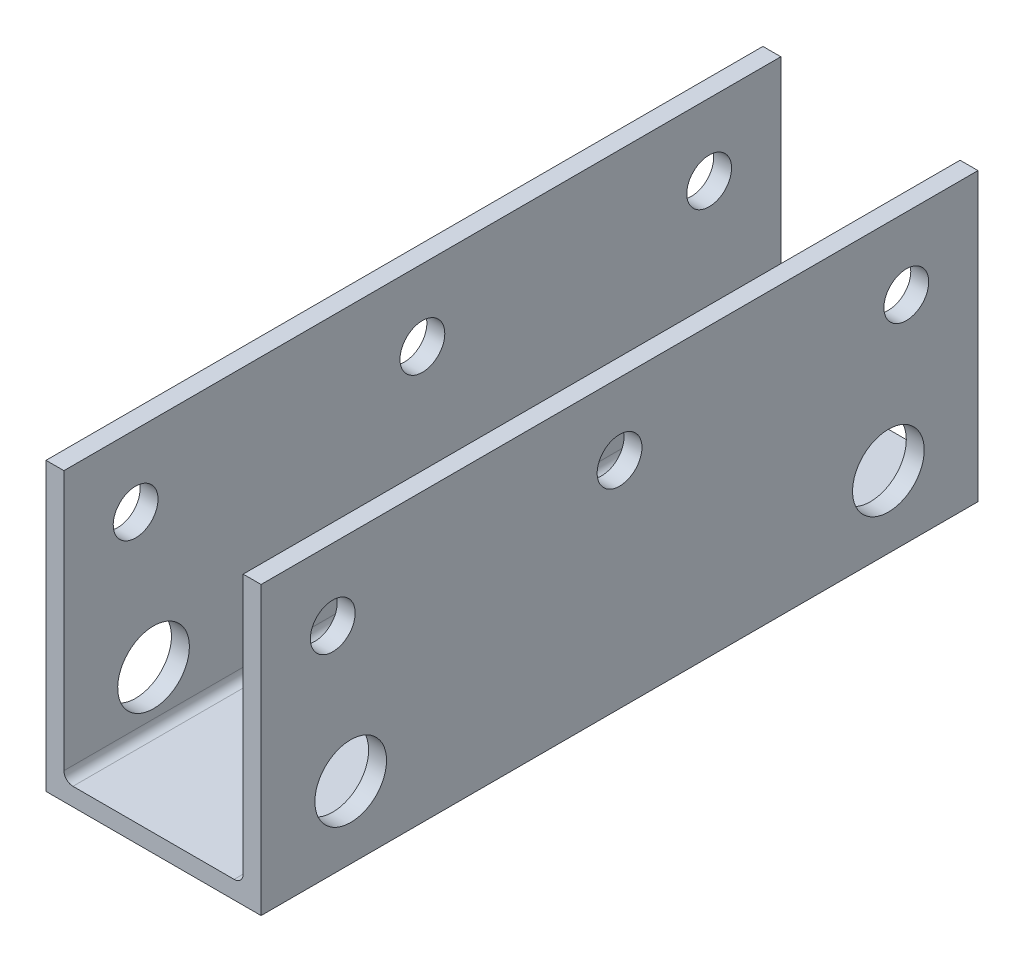
SolidWorks part; units mm, degrees
material "6061-T6 (SS)"
ref_plane "Front Plane" through (0, 0, 0) normal (0, 0, 1) x (1, 0, 0)
ref_plane "Top Plane" through (0, 0, 0) normal (0, 1, 0) x (1, 0, 0)
ref_plane "Right Plane" through (0, 0, 0) normal (1, 0, 0) x (0, 0, -1)
sketch "Sketch1" plane through (0, 0, 0) normal (0, 0, 1) x (1, 0, 0)
  line L0 (3.175, 50.8) -> (3.175, 3.175)
  line L1 (0, 0) -> (38.1, 0)
  line L2 (0, 0) -> (0, 50.8)
  line L3 (0, 50.8) -> (3.175, 50.8)
  line L4 (38.1, 0) -> (38.1, 50.8)
  line L5 (3.175, 3.175) -> (34.925, 3.175)
  line L6 (34.925, 3.175) -> (34.925, 50.8)
  line L7 (34.925, 50.8) -> (38.1, 50.8)
  dimension "D1" = 3.175
  dimension "D2" = 3.175
  dimension "D3" = 3.175
  dimension "D4" = 38.1
  dimension "D5" = 50.8
extrude "Boss-Extrude1" add sketch "Sketch1" along normal blind 127
sketch "Sketch2" plane through (38.1, 0, 0) normal (1, 0, 0) x (0, 0, -1)
  line L0 (0, 0) -> (0, 50.8) construction
  line L1 (-127, 0) -> (0, 0) construction
  line L2 (-114.3, 38.1) -> (-12.7, 38.1) construction
  line L3 (-127, 50.8) -> (0, 50.8) construction
  line L4 (-127, 0) -> (-127, 50.8) construction
  circle A0 centre (-15.875, 12.7) radius 6.35
  circle A1 centre (-111.125, 12.7) radius 6.35
  circle A2 centre (-114.3, 38.1) radius 3.9687
  circle A3 centre (-63.5, 38.1) radius 3.9688
  circle A4 centre (-12.7, 38.1) radius 3.9688
  point P20 (-63.5, 38.1)
  dimension "D2" = 12.7
  dimension "D9" = 7.9375
  dimension "D10" = 12.7
  dimension "D1" = 95.25
  dimension "D3" = 15.875
  dimension "D4" = 12.7
  dimension "D5" = 12.7
  dimension "D6" = 12.7
  dimension "D7" = 12.7
  dimension "D8" = 12.7
extrude "Cut-Extrude1" cut sketch "Sketch2" against normal blind 152.4
fillet "Fillet1" radius 1.6002 2 edges at (3.175, 3.175, 63.5) (34.925, 3.175, 63.5)
